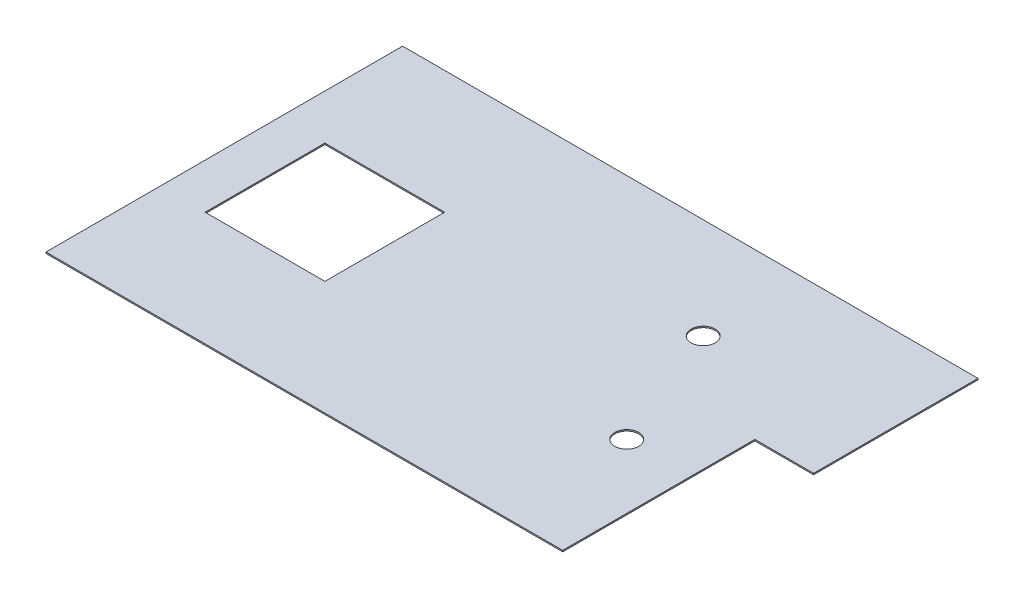
SolidWorks part; units mm, degrees
material "Balsa"
ref_plane "Front Plane" through (0, 0, 0) normal (0, 0, 1) x (1, 0, 0)
ref_plane "Top Plane" through (0, 0, 0) normal (0, 1, 0) x (1, 0, 0)
ref_plane "Right Plane" through (0, 0, 0) normal (1, 0, 0) x (0, 0, -1)
sketch "Sketch1" plane through (0, 0, 0) normal (0, 1, 0) x (1, 0, 0)
  line L0 (1369.06, 66.04) -> (1089.66, 66.04)
  line L1 (-1369.06, -848.36) -> (1089.66, -848.36)
  line L2 (-1369.06, -848.36) -> (-1369.06, 848.36)
  line L3 (-1369.06, 848.36) -> (1369.06, 848.36)
  line L4 (1369.06, 66.04) -> (1369.06, 848.36)
  line L5 (-1369.06, -848.36) -> (1369.06, 848.36) construction
  line L6 (-1369.06, 848.36) -> (1089.66, -675.2253) construction
  line L7 (1089.66, 66.04) -> (1089.66, -848.36)
  line L9 (-1154.43, 264.16) -> (-584.454, 264.16)
  line L10 (-1154.43, 264.16) -> (-1154.43, -305.816)
  line L11 (-1154.43, -305.816) -> (-584.454, -305.816)
  line L12 (-584.454, 264.16) -> (-584.454, -305.816)
  line L13 (-1154.43, 264.16) -> (-584.454, -305.816) construction
  line L14 (-1154.43, -305.816) -> (-584.454, 264.16) construction
  circle A0 centre (540.512, 369.316) radius 57.15
  circle A1 centre (784.86, -238.76) radius 57.15
  point P0 (0, 0)
  point P9 (-869.442, -20.828)
  dimension "D10" = 114.3
  dimension "D11" = 114.3
  dimension "D1" = 1696.72
  dimension "D2" = 2738.12
  dimension "D3" = 279.4
  dimension "D4" = 914.4
  dimension "D5" = 214.63
  dimension "D6" = 584.2
  dimension "D7" = 569.976
  dimension "D8" = 569.976
  dimension "D9" = 173.1347
  dimension "D12" = 828.548
  dimension "D13" = 479.044
  dimension "D14" = 304.8
  dimension "D15" = 609.6
extrude "Boss-Extrude1" add sketch "Sketch1" along normal blind 6.35
